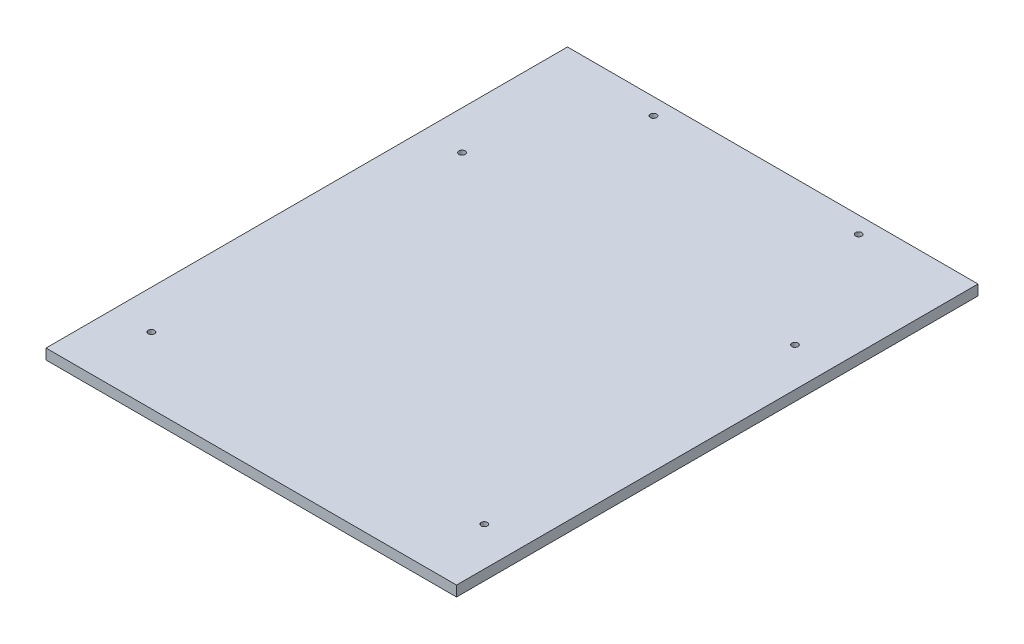
SolidWorks part; units mm, degrees
material "Pine"
ref_plane "Front Plane" through (0, 0, 0) normal (0, 0, 1) x (1, 0, 0)
ref_plane "Top Plane" through (0, 0, 0) normal (0, 1, 0) x (1, 0, 0)
ref_plane "Right Plane" through (0, 0, 0) normal (1, 0, 0) x (0, 0, -1)
sketch "Sketch1" plane through (0, 0, 0) normal (0, 1, 0) x (1, 0, 0)
  line L1 (-234.95, -298.45) -> (234.95, -298.45)
  line L2 (-234.95, -298.45) -> (-234.95, 298.45)
  line L3 (-234.95, 298.45) -> (234.95, 298.45)
  line L4 (234.95, -298.45) -> (234.95, 298.45)
  line L5 (-234.95, -298.45) -> (234.95, 298.45) construction
  line L6 (-234.95, 298.45) -> (234.95, -298.45) construction
  point P0 (0, 0)
  dimension "D1" = 469.9
  dimension "D2" = 596.9
extrude "Boss-Extrude1" add sketch "Sketch1" along normal blind 11.9062
sketch "Sketch2" plane through (0, 11.9062, 0) normal (0, 1, 0) x (1, 0, 0)
  line L0 (-234.95, -298.45) -> (234.95, -298.45) construction
  line L1 (234.95, 298.45) -> (-234.95, 298.45) construction
  point P0 (-190.5, -222.25)
  point P1 (190.5, -222.25)
  point P2 (190.5, 133.35)
  point P3 (-190.5, 133.35)
  point P4 (117.475, 279.4)
  point P8 (-117.475, 279.4)
  dimension "D1" = 381
  dimension "D2" = 190.5
  dimension "D3" = 355.6
  dimension "D4" = 76.2
  dimension "D5" = 234.95
  dimension "D6" = 117.475
  dimension "D7" = 19.05
hole_wizard "9/32 (0.28125) Diameter Hole1" positions "Sketch3" profile "Sketch4" hole size "9/32" standard "ANSI Inch" end condition through all
sketch "Sketch3" plane through (0, 11.9062, 0) normal (0, 1, 0) x (1, 0, 0)
  point P0 (-190.5, 133.35)
  point P3 (190.5, 133.35)
  point P6 (190.5, -222.25)
  point P9 (-190.5, -222.25)
  point P13 (-117.475, 279.4)
  point P16 (117.475, 279.4)
sketch "Sketch4" plane through (-190.5, 11.9062, -133.35) normal (1, 0, 0) x (0, 0, 1)
  line L0 (0, 0) -> (0, 11.9062)
  line L1 (0, 11.9062) -> (3.5719, 11.9062)
  line L2 (3.5719, 11.9062) -> (3.5719, 0)
  line L5 (3.5719, 0) -> (0, 0)
  line L11 (0, -6.35) -> (0, 107.95) construction
  dimension "Thru Hole Dia." = 7.1437
  dimension "Thru Hole Depth" = 11.9062
